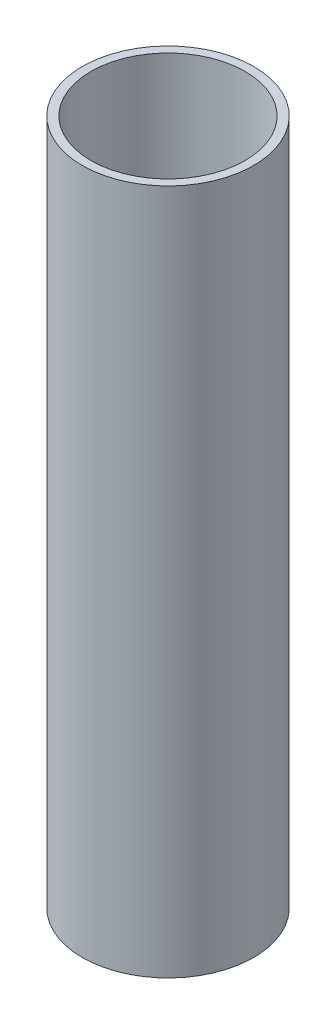
SolidWorks part; units mm, degrees
ref_plane "Front Plane" through (0, 0, 0) normal (0, 0, 1) x (1, 0, 0)
ref_plane "Top Plane" through (0, 0, 0) normal (0, 1, 0) x (1, 0, 0)
ref_plane "Right Plane" through (0, 0, 0) normal (1, 0, 0) x (0, 0, -1)
sketch "Sketch1" plane through (0, 0, 0) normal (0, 1, 0) x (1, 0, 0)
  circle A0 centre (0, 0) radius 22.5
  circle A1 centre (0, 0) radius 25
  dimension "D1" = 50
  dimension "D2" = 45
extrude "Boss-Extrude1" add sketch "Sketch1" along normal blind 200
